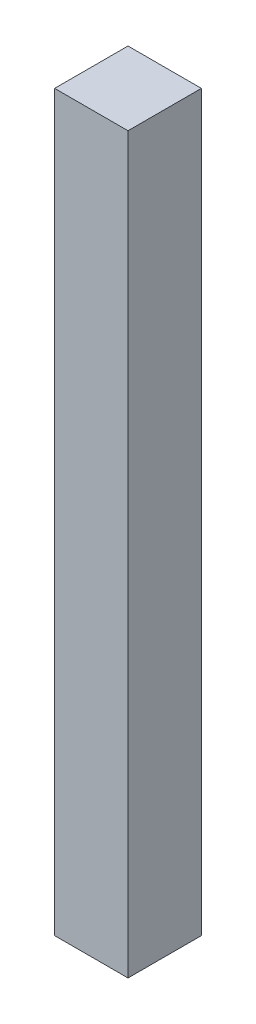
SolidWorks part; units mm, degrees
ref_plane "Front Plane" through (0, 0, 0) normal (0, 0, 1) x (1, 0, 0)
ref_plane "Top Plane" through (0, 0, 0) normal (0, 1, 0) x (1, 0, 0)
ref_plane "Right Plane" through (0, 0, 0) normal (1, 0, 0) x (0, 0, -1)
sketch "Sketch1" plane through (0, 0, 0) normal (0, 1, 0) x (1, 0, 0)
  line L1 (0, 0) -> (100, 0)
  line L2 (0, 0) -> (0, 100)
  line L3 (0, 100) -> (100, 100)
  line L4 (100, 0) -> (100, 100)
  dimension "D1" = 100
  dimension "D2" = 100
extrude "Boss-Extrude1" add sketch "Sketch1" along normal blind 1000
